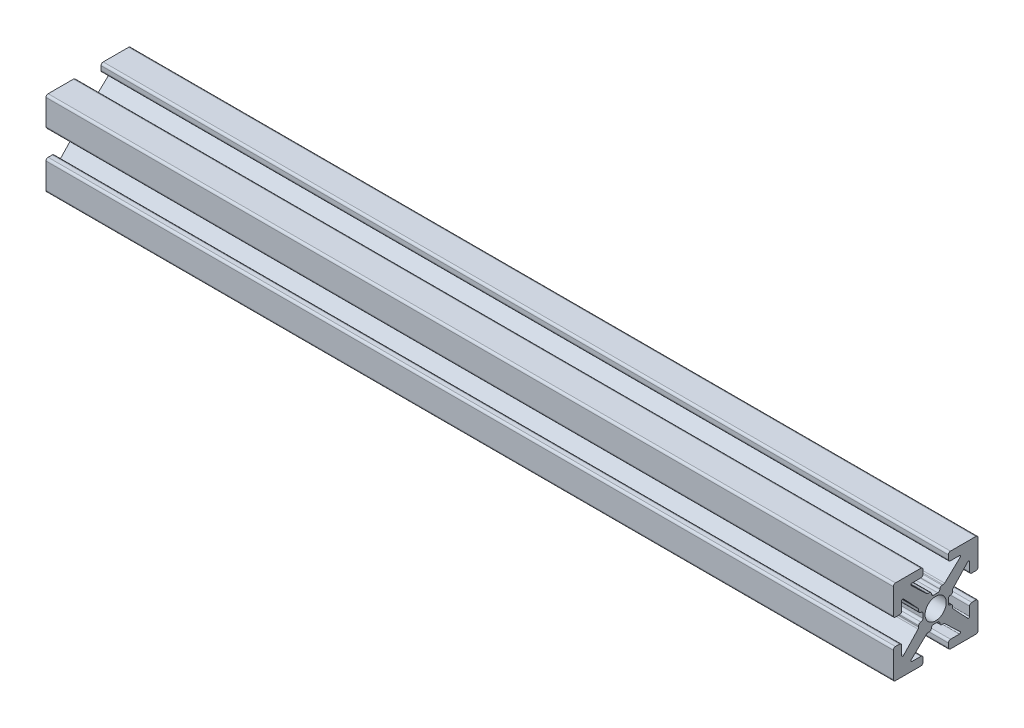
SolidWorks part; units mm, degrees
material "1060 Сплав"
ref_plane "Front Plane" through (0, 0, 0) normal (0, 0, 1) x (1, 0, 0)
ref_plane "Top Plane" through (0, 0, 0) normal (0, 1, 0) x (1, 0, 0)
ref_plane "Right Plane" through (0, 0, 0) normal (1, 0, 0) x (0, 0, -1)
sketch "Sketch1" plane through (0, 0, 0) normal (1, 0, 0) x (0, 0, -1)
  line L0 (0, 0) -> (0, 1.4948) construction
  line L1 (-0.2413, 1.4948) -> (0.2413, 1.4948)
  line L2 (5, 1.7526) -> (5, 4.746)
  line L3 (0.7493, 2.0028) -> (0.8899, 2.0028)
  line L4 (1.0639, 2.0718) -> (2.8908, 3.7899)
  line L5 (2.8038, 4.0094) -> (1.7526, 4.0094)
  line L6 (1.4986, 4.2634) -> (1.4986, 4.746)
  line L7 (1.7526, 5) -> (4.746, 5)
  line L8 (5, 5) -> (0, 0) construction
  line L9 (0, 0) -> (8.6271, 0) construction
  line L10 (0, 0) -> (0, 5) construction
  line L11 (4.2634, 1.4986) -> (4.746, 1.4986)
  line L12 (4.0094, 2.8038) -> (4.0094, 1.7526)
  line L13 (2.0718, 1.0639) -> (3.7899, 2.8908)
  line L14 (2.0028, 0.7493) -> (2.0028, 0.8899)
  line L15 (1.4948, -0.2413) -> (1.4948, 0.2413)
  line L16 (0, 0) -> (1.4948, 0) construction
  line L17 (-0.2413, -1.4948) -> (0.2413, -1.4948)
  line L18 (0.7493, -2.0028) -> (0.8899, -2.0028)
  line L19 (1.0639, -2.0718) -> (2.8908, -3.7899)
  line L20 (2.8038, -4.0094) -> (1.7526, -4.0094)
  line L21 (1.4986, -4.2634) -> (1.4986, -4.746)
  line L22 (1.7526, -5) -> (4.746, -5)
  line L23 (5, -1.7526) -> (5, -4.746)
  line L24 (4.2634, -1.4986) -> (4.746, -1.4986)
  line L25 (4.0094, -2.8038) -> (4.0094, -1.7526)
  line L26 (2.0718, -1.0639) -> (3.7899, -2.8908)
  line L27 (2.0028, -0.7493) -> (2.0028, -0.8899)
  line L28 (-0.7493, 2.0028) -> (-0.8899, 2.0028)
  line L29 (-1.0639, 2.0718) -> (-2.8908, 3.7899)
  line L30 (-2.8038, 4.0094) -> (-1.7526, 4.0094)
  line L31 (-1.4986, 4.2634) -> (-1.4986, 4.746)
  line L32 (-1.7526, 5) -> (-4.746, 5)
  line L33 (-5, 1.7526) -> (-5, 4.746)
  line L34 (-4.2634, 1.4986) -> (-4.746, 1.4986)
  line L35 (-4.0094, 2.8038) -> (-4.0094, 1.7526)
  line L36 (-2.0718, 1.0639) -> (-3.7899, 2.8908)
  line L37 (-2.0028, 0.7493) -> (-2.0028, 0.8899)
  line L38 (-1.4948, -0.2413) -> (-1.4948, 0.2413)
  line L39 (-2.0028, -0.7493) -> (-2.0028, -0.8899)
  line L40 (-2.0718, -1.0639) -> (-3.7899, -2.8908)
  line L41 (-4.0094, -2.8038) -> (-4.0094, -1.7526)
  line L42 (-4.2634, -1.4986) -> (-4.746, -1.4986)
  line L43 (-5, -1.7526) -> (-5, -4.746)
  line L44 (-1.7526, -5) -> (-4.746, -5)
  line L45 (-1.4986, -4.2634) -> (-1.4986, -4.746)
  line L46 (-2.8038, -4.0094) -> (-1.7526, -4.0094)
  line L47 (-1.0639, -2.0718) -> (-2.8908, -3.7899)
  line L48 (-0.7493, -2.0028) -> (-0.8899, -2.0028)
  arc A0 (2.8908, 3.7899) -> (2.8038, 4.0094) centre (2.8038, 3.8824) ccw
  arc A1 (0.4953, 1.7488) -> (0.7493, 2.0028) centre (0.7493, 1.7488) cw
  arc A2 (0.8899, 2.0028) -> (1.0639, 2.0718) centre (0.8899, 2.2568) ccw
  arc A3 (1.7526, 4.0094) -> (1.4986, 4.2634) centre (1.7526, 4.2634) cw
  arc A4 (1.4986, 4.746) -> (1.7526, 5) centre (1.7526, 4.746) cw
  arc A5 (0.2413, 1.4948) -> (0.4953, 1.7488) centre (0.2413, 1.7488) ccw
  arc A6 (4.746, 1.4986) -> (5, 1.7526) centre (4.746, 1.7526) ccw
  arc A7 (4.0094, 1.7526) -> (4.2634, 1.4986) centre (4.2634, 1.7526) ccw
  arc A8 (3.7899, 2.8908) -> (4.0094, 2.8038) centre (3.8824, 2.8038) cw
  arc A9 (2.0028, 0.8899) -> (2.0718, 1.0639) centre (2.2568, 0.8899) cw
  arc A10 (1.7488, 0.4953) -> (2.0028, 0.7493) centre (1.7488, 0.7493) ccw
  arc A11 (1.4948, 0.2413) -> (1.7488, 0.4953) centre (1.7488, 0.2413) cw
  arc A12 (0.2413, -1.4948) -> (0.4953, -1.7488) centre (0.2413, -1.7488) cw
  arc A13 (0.4953, -1.7488) -> (0.7493, -2.0028) centre (0.7493, -1.7488) ccw
  arc A14 (0.8899, -2.0028) -> (1.0639, -2.0718) centre (0.8899, -2.2568) cw
  arc A15 (2.8908, -3.7899) -> (2.8038, -4.0094) centre (2.8038, -3.8824) cw
  arc A16 (1.7526, -4.0094) -> (1.4986, -4.2634) centre (1.7526, -4.2634) ccw
  arc A17 (1.4986, -4.746) -> (1.7526, -5) centre (1.7526, -4.746) ccw
  arc A18 (4.746, -1.4986) -> (5, -1.7526) centre (4.746, -1.7526) cw
  arc A19 (4.0094, -1.7526) -> (4.2634, -1.4986) centre (4.2634, -1.7526) cw
  arc A20 (3.7899, -2.8908) -> (4.0094, -2.8038) centre (3.8824, -2.8038) ccw
  arc A21 (2.0028, -0.8899) -> (2.0718, -1.0639) centre (2.2568, -0.8899) ccw
  arc A22 (1.7488, -0.4953) -> (2.0028, -0.7493) centre (1.7488, -0.7493) cw
  arc A23 (1.4948, -0.2413) -> (1.7488, -0.4953) centre (1.7488, -0.2413) ccw
  arc A24 (-0.2413, 1.4948) -> (-0.4953, 1.7488) centre (-0.2413, 1.7488) cw
  arc A25 (-0.4953, 1.7488) -> (-0.7493, 2.0028) centre (-0.7493, 1.7488) ccw
  arc A26 (-0.8899, 2.0028) -> (-1.0639, 2.0718) centre (-0.8899, 2.2568) cw
  arc A27 (-2.8908, 3.7899) -> (-2.8038, 4.0094) centre (-2.8038, 3.8824) cw
  arc A28 (-1.7526, 4.0094) -> (-1.4986, 4.2634) centre (-1.7526, 4.2634) ccw
  arc A29 (-1.4986, 4.746) -> (-1.7526, 5) centre (-1.7526, 4.746) ccw
  arc A30 (-4.746, 1.4986) -> (-5, 1.7526) centre (-4.746, 1.7526) cw
  arc A31 (-4.0094, 1.7526) -> (-4.2634, 1.4986) centre (-4.2634, 1.7526) cw
  arc A32 (-3.7899, 2.8908) -> (-4.0094, 2.8038) centre (-3.8824, 2.8038) ccw
  arc A33 (-2.0028, 0.8899) -> (-2.0718, 1.0639) centre (-2.2568, 0.8899) ccw
  arc A34 (-1.7488, 0.4953) -> (-2.0028, 0.7493) centre (-1.7488, 0.7493) cw
  arc A35 (-1.4948, 0.2413) -> (-1.7488, 0.4953) centre (-1.7488, 0.2413) ccw
  arc A36 (-1.4948, -0.2413) -> (-1.7488, -0.4953) centre (-1.7488, -0.2413) cw
  arc A37 (-1.7488, -0.4953) -> (-2.0028, -0.7493) centre (-1.7488, -0.7493) ccw
  arc A38 (-2.0028, -0.8899) -> (-2.0718, -1.0639) centre (-2.2568, -0.8899) cw
  arc A39 (-3.7899, -2.8908) -> (-4.0094, -2.8038) centre (-3.8824, -2.8038) cw
  arc A40 (-4.0094, -1.7526) -> (-4.2634, -1.4986) centre (-4.2634, -1.7526) ccw
  arc A41 (-4.746, -1.4986) -> (-5, -1.7526) centre (-4.746, -1.7526) ccw
  arc A42 (-1.4986, -4.746) -> (-1.7526, -5) centre (-1.7526, -4.746) cw
  arc A43 (-1.7526, -4.0094) -> (-1.4986, -4.2634) centre (-1.7526, -4.2634) cw
  arc A44 (-2.8908, -3.7899) -> (-2.8038, -4.0094) centre (-2.8038, -3.8824) ccw
  arc A45 (-0.8899, -2.0028) -> (-1.0639, -2.0718) centre (-0.8899, -2.2568) ccw
  arc A46 (-0.4953, -1.7488) -> (-0.7493, -2.0028) centre (-0.7493, -1.7488) cw
  arc A47 (-0.2413, -1.4948) -> (-0.4953, -1.7488) centre (-0.2413, -1.7488) ccw
  arc A48 (-4.746, 5) -> (-5, 4.746) centre (-4.746, 4.746) ccw
  arc A49 (-5, -4.746) -> (-4.746, -5) centre (-4.746, -4.746) ccw
  arc A50 (4.746, -5) -> (5, -4.746) centre (4.746, -4.746) ccw
  arc A51 (4.746, 5) -> (5, 4.746) centre (4.746, 4.746) cw
  point P14 (3.1242, 4.0094)
  point P19 (0.9906, 2.0028)
  point P150 (0, -1.4948)
  point P152 (-5, 5)
  point P155 (-5, -5)
  point P158 (5, -5)
  dimension "D10" = 0.127
  dimension "D11" = 0.254
  dimension "D2" = 0.254
  dimension "D1" = 10
  dimension "D3" = 2.9972
  dimension "D4" = 0.508
  dimension "D5" = 2.9972
  dimension "D6" = 0.9906
  dimension "D7" = 1.6256
  dimension "D8" = 1.9812
  dimension "D9" = 0.9906
extrude "Estrusione-Estrusione1" add sketch "Sketch1" along normal blind 100 contours L36 A32 L35 A31 L34 A30 L33 A48 L32 A29 L31 A28 L30 A27 L29 A26 L28 A25 A24 L1 A5 A1 L3 A2 L4 A0 L5 A3 L6 A4 L7 A51 L2 A6 L11 A7 L12 A8 L13 A9 L14 A10 A11 L15 A23 A22 L27 A21 L26 A20 L25 A19 L24 A18 L23 A50 L22 A17 L21 A16 L20 A15 L19 A14 L18 A13 A12 L17 A47 A46 L48 A45 L47 A44 L46 A43 L45 A42 L44 A49 L43 A41 L42 A40 L41 A39 L40 A38 L39 A37 A36 L38 A35 A34 L37 A33
hole_wizard "Foro filettato M3x0.5-1" positions "Schizzo2" profile "Schizzo1" tap size "M3x0.5" standard "Ansi Metric" end condition through all
sketch "Schizzo2" plane through (0, 0, 0) normal (-1, 0, 0) x (0, 0, 1)
  point P0 (0, 0)
sketch "Schizzo1" plane through (0, 0, 0) normal (0, 1, 0) x (0, 0, 1)
  line L0 (0, 0) -> (0, 100)
  line L1 (0, 100) -> (1.25, 100)
  line L2 (1.25, 100) -> (1.25, 0)
  line L5 (1.25, 0) -> (0, 0)
  line L11 (0, -6.35) -> (0, 107.95) construction
  dimension "Thread Major Dia." = 2.5
  dimension "Thru Tap Drill Depth" = 100
equation "\"camera plate width\"=220"
equation "\"camera plate length\"=220"
equation "\"camera height\"= 100"
equation "\"D1@Estrusione-Estrusione1\"=\"camera height\""
equation "\"zero height\"= 100"
